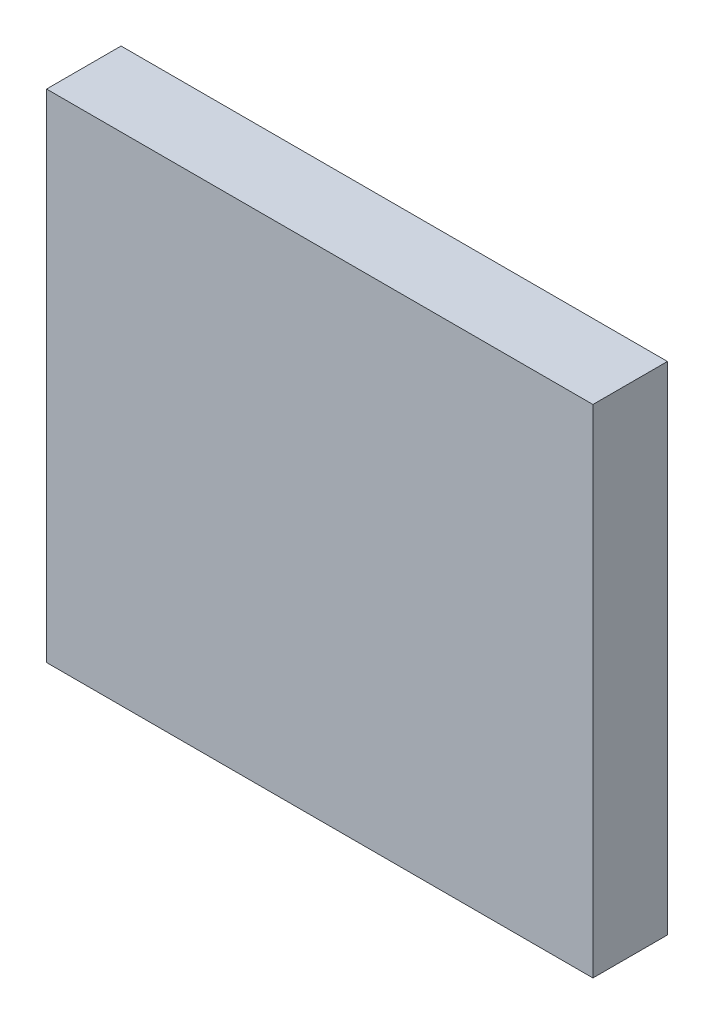
SolidWorks part; units mm, degrees
ref_plane "Front Plane" through (0, 0, 0) normal (0, 0, 1) x (1, 0, 0)
ref_plane "Top Plane" through (0, 0, 0) normal (0, 1, 0) x (1, 0, 0)
ref_plane "Right Plane" through (0, 0, 0) normal (1, 0, 0) x (0, 0, -1)
sketch "Sketch1" plane through (0, 0, 0) normal (0, 0, 1) x (1, 0, 0)
  line L0 (-295.8261, 0) -> (390.5534, 0) construction
  line L1 (0, -271.3636) -> (0, 570.3327) construction
  line L3 (0, 0) -> (82.5, 0)
  line L4 (0, 0) -> (0, 75)
  line L5 (0, 75) -> (82.5, 75)
  line L6 (82.5, 0) -> (82.5, 75)
  dimension "D1" = 75
  dimension "D2" = 82.5
extrude "Boss-Extrude1" add sketch "Sketch1" along normal blind 11.25
sketch "Sketch2" plane through (0, 0, 0) normal (0, 0, -1) x (-1, 0, 0)
  line L0 (0, 75) -> (0, 0) construction
  line L1 (-79.5, 72) -> (-3, 72)
  line L2 (-79.5, 72) -> (-79.5, 3)
  line L3 (-79.5, 3) -> (-3, 3)
  line L4 (-3, 72) -> (-3, 3)
  line L5 (0, 0) -> (-82.5, 0) construction
  line L6 (-82.5, 0) -> (-82.5, 75) construction
  line L7 (-82.5, 75) -> (0, 75) construction
  dimension "D1" = 3
  dimension "D2" = 3
  dimension "D3" = 3
  dimension "D4" = 3
extrude "Cut-Extrude1" cut sketch "Sketch2" against normal blind 9.25
